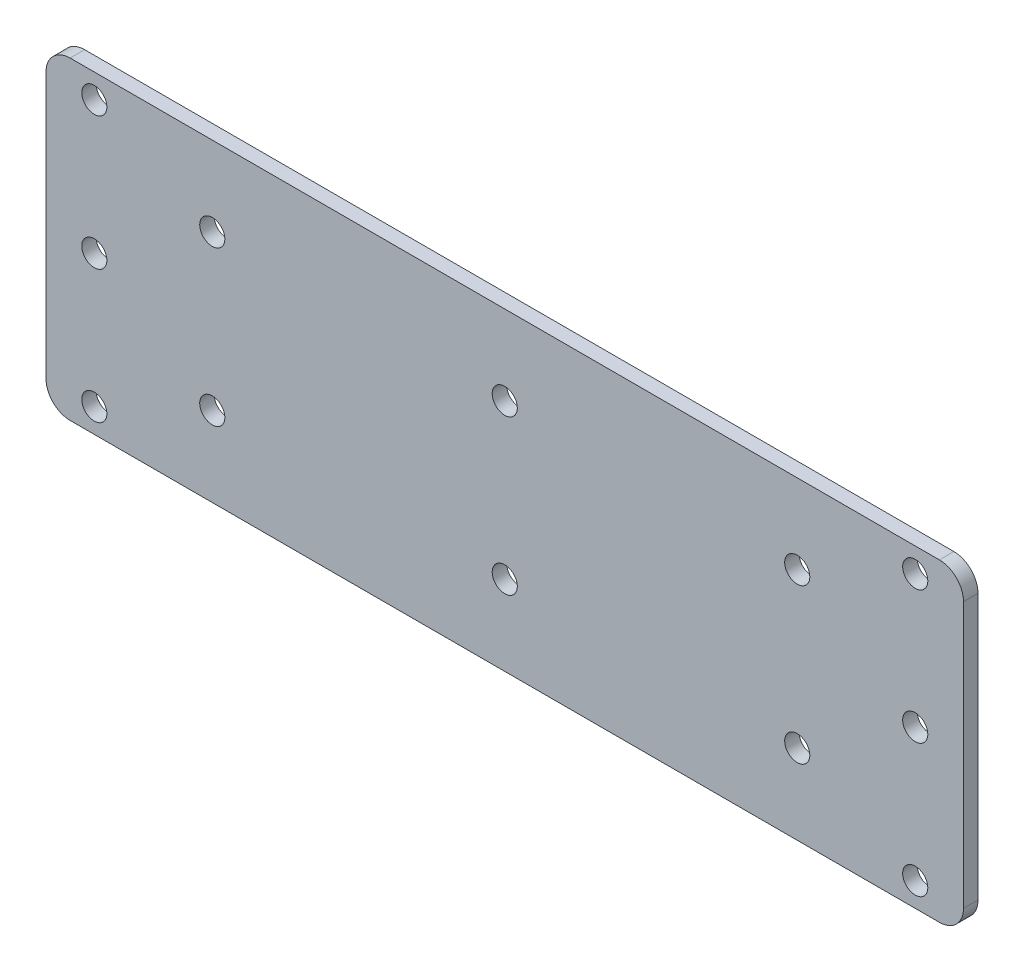
SolidWorks part; units mm, degrees
ref_plane "前视基准面" through (0, 0, 0) normal (0, 0, 1) x (1, 0, 0)
ref_plane "上视基准面" through (0, 0, 0) normal (0, 1, 0) x (1, 0, 0)
ref_plane "右视基准面" through (0, 0, 0) normal (1, 0, 0) x (0, 0, -1)
sketch "草图1" plane through (0, 0, 0) normal (0, 0, 1) x (1, 0, 0)
  line L1 (-125, 32.5) -> (125, 32.5)
  line L2 (-125, 32.5) -> (-125, -32.5)
  line L3 (-125, -32.5) -> (125, -32.5)
  line L4 (125, 32.5) -> (125, -32.5)
  line L5 (-125, 32.5) -> (125, -32.5) construction
  line L6 (-125, -32.5) -> (125, 32.5) construction
  circle A4 centre (-70, 16) radius 2.5
  circle A5 centre (-70, -16) radius 2.5
  circle A6 centre (70, -16) radius 2.5
  circle A7 centre (70, 16) radius 2.5
  circle A15 centre (0, 16) radius 2.5
  circle A16 centre (0, -16) radius 2.5
  point P0 (0, 0)
  dimension "D5" = 16
  dimension "D11" = 5
  dimension "D12" = 5
  dimension "D16" = 5
  dimension "D17" = 5
  dimension "D1" = 250
  dimension "D2" = 65
  dimension "D4" = 32
  dimension "D13" = 70
extrude "凸台-拉伸1" add sketch "草图1" along normal blind 3
fillet "圆角1" radius 3 4 edges at (125, -32.5, 1.5) (125, 32.5, 1.5) (-125, -32.5, 1.5) (-125, 32.5, 1.5)
sketch "草图4" plane through (0, 0, 0) normal (0, 0, -1) x (-1, 0, 0)
  line L0 (-125, 29.5) -> (-113.82, 29.5) construction
  line L1 (-113.82, 29.5) -> (-113.82, 32.5) construction
  line L2 (-122, 32.5) -> (122, 32.5) construction
  line L3 (-113.82, 32.5) -> (-122, 32.5)
  line L4 (-125, 29.5) -> (-125, -29.5)
  line L5 (-113.82, 32.5) -> (-113.82, -32.5)
  line L6 (122, -32.5) -> (-122, -32.5) construction
  line L7 (-113.82, -32.5) -> (-122, -32.5)
  arc A0 (-122, 32.5) -> (-125, 29.5) centre (-122, 29.5) ccw
  arc A1 (-125, -29.5) -> (-122, -32.5) centre (-122, -29.5) ccw
  dimension "D1" = 3
  dimension "D2" = 3
extrude "切除-拉伸3" cut sketch "草图4" against normal through all
fillet "圆角2" radius 3 2 edges at (113.82, 32.5, 1.5) (113.82, -32.5, 1.5)
sketch "草图6" plane through (0, 0, 3) normal (0, 0, 1) x (1, 0, 0)
  line L1 (-95, -32.5) -> (-95, 32.5)
  line L2 (-122, -32.5) -> (110.82, -32.5) construction
  line L3 (110.82, 32.5) -> (-122, 32.5) construction
  line L4 (-95, 32.5) -> (-125, 32.5)
  line L5 (-125, 32.5) -> (-125, -32.5)
  line L6 (-125, -32.5) -> (-95, -32.5)
extrude "切除-拉伸4" cut sketch "草图6" against normal blind 5
sketch "草图7" plane through (0, 0, 3) normal (0, 0, 1) x (1, 0, 0)
  line L0 (113.82, -32.8603) -> (113.82, 33.557)
  line L1 (113.82, 33.557) -> (94.9962, 32.5)
  line L2 (-95, -32.5) -> (110.82, -32.5) construction
  line L3 (94.9962, -32.5) -> (94.9962, 32.5)
  line L4 (110.82, 32.5) -> (-95, 32.5) construction
  line L6 (94.9962, -32.5) -> (113.82, -32.8603)
extrude "切除-拉伸7" cut sketch "草图7" against normal blind 5
fillet "圆角3" radius 5 4 edges at (-95, -32.5, 1.5) (-95, 32.5, 1.5) (94.9962, 32.5, 1.5) (94.9962, -32.5, 1.5)
sketch "草图8" plane through (0, 0, 0) normal (0, 0, -1) x (-1, 0, 0)
  circle A0 centre (70, 16) radius 2.5
  circle A1 centre (70, -16) radius 2.5
  circle A2 centre (-70, 16) radius 2.5
  circle A3 centre (-70, -16) radius 2.5
extrude "凸台-拉伸2" add sketch "草图8" against normal blind 3
sketch "草图10" plane through (0, 0, 0) normal (0, 0, -1) x (-1, 0, 0)
  circle A0 centre (-60.5639, 16.0292) radius 2.5
  circle A1 centre (-60.5639, -15.9708) radius 2.5
  circle A2 centre (62.8941, 16.0292) radius 2.5
  circle A3 centre (62.8941, -15.9708) radius 2.5
extrude "切除-拉伸8" cut sketch "草图10" against normal blind 3
sketch "草图13" plane through (0, 0, 0) normal (0, 0, -1) x (-1, 0, 0)
  line L0 (0, 16) -> (95, 16) construction
  line L1 (95, -27.5) -> (95, 27.5) construction
  circle A0 centre (62.8941, 16.0292) radius 2.5
  circle A1 centre (62.8941, -15.9708) radius 2.5
extrude "凸台-拉伸3" add sketch "草图13" against normal up to surface (3 mm away) up to face at (58.0639, -15.9708, 3)
sketch "草图15" plane through (0, 0, 0) normal (0, 0, -1) x (-1, 0, 0)
  circle A0 centre (62.8941, 16.0292) radius 2.5
  circle A1 centre (62.8941, -15.9708) radius 2.5
extrude "凸台-拉伸4" add sketch "草图15" against normal blind 3
sketch "草图18" plane through (0, 0, 0) normal (0, 0, -1) x (-1, 0, 0)
  circle A0 centre (-84.9962, 27.5) radius 2.5
  circle A1 centre (-84.9962, -27.5) radius 2.5
  dimension "D1" = 5
extrude "切除-拉伸11" cut sketch "草图18" against normal through all
ref_plane "基准面1" through (-0.0019, 0, 0) normal (1, 0, 0) x (0, 0, -1)
mirror "镜向1" about plane through (-0.0019, 0, 0) normal (1, 0, 0) of "切除-拉伸11"
sketch "草图20" plane through (0, 0, 0) normal (0, 0, -1) x (-1, 0, 0)
  circle A0 centre (85, 0) radius 2.5
  circle A1 centre (-84.9962, 0) radius 2.5
extrude "切除-拉伸12" cut sketch "草图20" against normal blind 10 contours A1 | A0
sketch "草图21" plane through (0, 0, 0) normal (0, 0, -1) x (-1, 0, 0)
  line L0 (0.0019, 1.65) -> (0.0019, -1.65) construction
  circle A0 centre (-84.9962, 27.5) radius 2.6
  circle A1 centre (-60.5639, 16.0292) radius 2.6
  circle A2 centre (-84.9962, 0) radius 2.6
  circle A3 centre (-60.5639, -15.9708) radius 2.6
  circle A4 centre (-84.9962, -27.5127) radius 2.6
  circle A5 centre (0.0019, 16.0292) radius 2.6
  circle A6 centre (0.0019, -15.9708) radius 2.6
  circle A9 centre (85, -27.5127) radius 2.6
  circle A10 centre (60.5678, -15.9708) radius 2.6
  circle A11 centre (85, 0) radius 2.6
  circle A12 centre (60.5678, 16.0292) radius 2.6
  circle A13 centre (85, 27.5) radius 2.6
  point P5 (-60.5639, 16.0292)
  point P9 (-84.9962, 0)
  point P13 (-60.5639, -15.9708)
  point P17 (-74.5832, -24.6982)
  point P18 (-84.2617, -27.3918)
  point P19 (-84.9962, -27.5127)
  point P22 (-28.6856, 16.0292)
  point P23 (0.0019, 16.0292)
  point P28 (0.0019, -15.9708)
  point P31 (54.644, 16.0292)
  point P32 (84.9636, 27.5)
  point P33 (84.9707, 27.5)
  point P36 (81.9814, 22.4128)
  point P37 (62.7813, 16.0292)
  point P38 (68.5817, 14.8557)
  point P39 (62.684, 15.9104)
  point P40 (62.8296, 15.9371)
  point P41 (62.9003, 16.0292)
  point P42 (0, 0)
  point P43 (85.0044, 27.5)
extrude "切除-拉伸13" cut sketch "草图21" against normal through all
